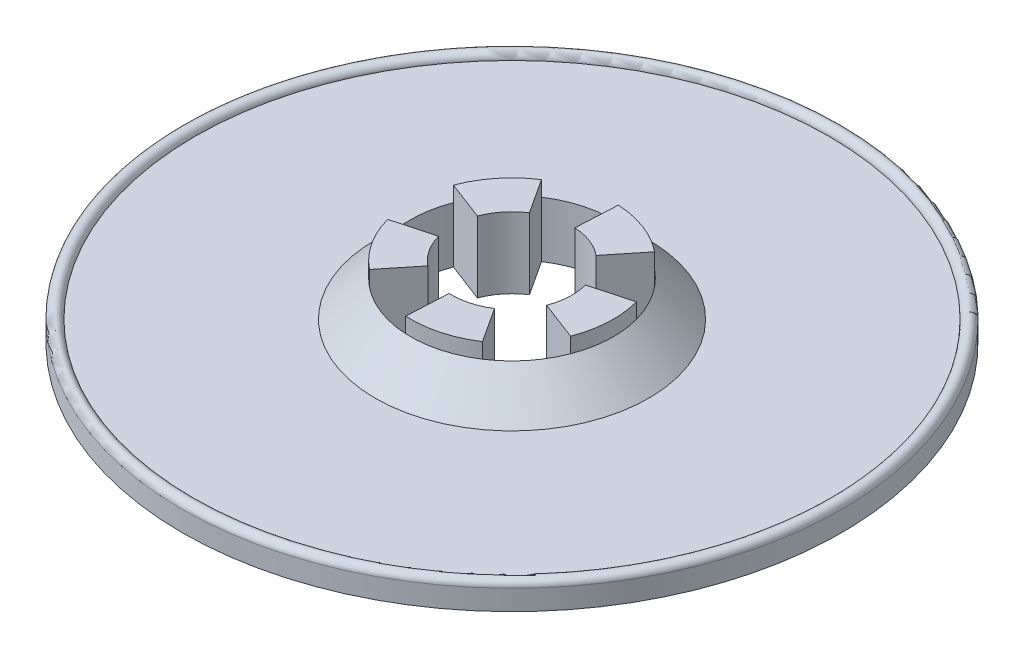
SolidWorks part; units mm, degrees
ref_plane "Front Plane" through (0, 0, 0) normal (0, 0, 1) x (1, 0, 0)
ref_plane "Top Plane" through (0, 0, 0) normal (0, 1, 0) x (1, 0, 0)
ref_plane "Right Plane" through (0, 0, 0) normal (1, 0, 0) x (0, 0, -1)
sketch "Sketch1" plane through (0, 0, 0) normal (0, 1, 0) x (1, 0, 0)
  circle A0 centre (0, 0) radius 41.275
  dimension "D1" = 82.55
extrude "Boss-Extrude1" add sketch "Sketch1" along normal blind 2.54
sketch "Sketch6" plane through (0, 2.54, 0) normal (0, 1, 0) x (1, 0, 0)
  circle A0 centre (0, 0) radius 12.7
  dimension "D1" = 25.4
extrude "Boss-Extrude3" add sketch "Sketch6" along normal blind 6.35
chamfer "Chamfer2" distance 4.445 angle 45 1 edges at (0, 2.54, 12.7)
sketch "Sketch4" plane through (0, 0, 0) normal (0, -1, 0) x (1, 0, 0)
  line L0 (6.9396, 10.6363) -> (4.0982, 6.2813)
  line L1 (11.8662, 4.526) -> (7.0076, 2.6728)
  line L2 (12.2602, -3.3132) -> (7.2403, -1.9566)
  line L3 (7.9713, -9.8868) -> (4.7075, -5.8387)
  line L4 (0.6376, -12.684) -> (0.3765, -7.4905)
  line L5 (-6.9396, -10.6363) -> (-4.0982, -6.2813)
  line L6 (-11.8662, -4.526) -> (-7.0076, -2.6728)
  line L7 (-12.2602, 3.3132) -> (-7.2403, 1.9566)
  line L10 (-7.9713, 9.8868) -> (-4.7075, 5.8387)
  line L11 (-0.6376, 12.684) -> (-0.3765, 7.4905)
  circle A0 centre (0, 0) radius 12.7 construction
  arc A1 (7.0076, 2.6728) -> (4.0982, 6.2813) centre (0, 0) ccw
  arc A2 (11.8662, 4.526) -> (6.9396, 10.6363) centre (0, 0) ccw
  arc A3 (4.7075, -5.8387) -> (7.2403, -1.9566) centre (0, 0) ccw
  arc A4 (7.9713, -9.8868) -> (12.2602, -3.3132) centre (0, 0) ccw
  arc A5 (-4.0982, -6.2813) -> (0.3765, -7.4905) centre (0, 0) ccw
  arc A6 (-6.9396, -10.6363) -> (0.6376, -12.684) centre (0, 0) ccw
  arc A7 (-7.2403, 1.9566) -> (-7.0076, -2.6728) centre (0, 0) ccw
  arc A8 (-12.2602, 3.3132) -> (-11.8662, -4.526) centre (0, 0) ccw
  arc A10 (-0.6376, 12.684) -> (-7.9713, 9.8868) centre (0, 0) ccw
  arc A13 (7.0076, 2.6728) -> (4.0982, 6.2813) centre (0, 0) ccw
  arc A14 (4.7075, -5.8387) -> (7.2403, -1.9566) centre (0, 0) ccw
  arc A16 (-4.0982, -6.2813) -> (0.3765, -7.4905) centre (0, 0) ccw
  arc A17 (-7.2403, 1.9566) -> (-7.0076, -2.6728) centre (0, 0) ccw
  circle A20 centre (0, 0) radius 7.5
  circle A21 centre (0, 0) radius 41.275 construction
  point P40 (0, 0)
  dimension "D1" = 36
  dimension "D2" = 7.5
  dimension "D3" = 12.7
extrude "Cut-Extrude2" cut sketch "Sketch4" against normal through all
sketch "Sketch7" plane through (0, 0, 0) normal (0, 0, 1) x (1, 0, 0)
  line L0 (41.275, 2.54) -> (-41.275, 2.54) construction
  line L1 (-41.275, 2.54) -> (-39.685, 2.54)
  arc A0 (-39.685, 2.54) -> (-41.275, 2.54) centre (-40.48, 2.54) ccw
  dimension "D1" = 1.59
ref_axis "Axis1" through (0, 8.001, 0) along (0, -1, 0)
revolve "Revolve1" add sketch "Sketch7" angle 360 about axis through (0, 8.001, 0) along (0, -1, 0)
